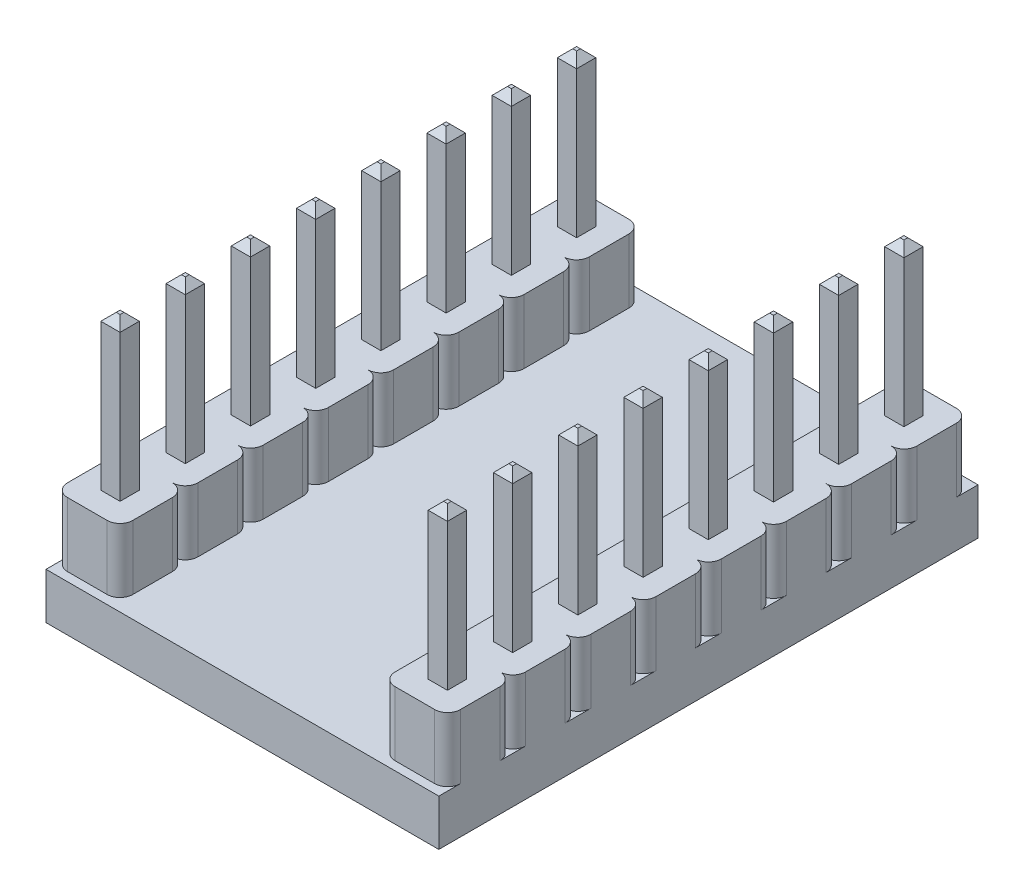
SolidWorks part; units mm, degrees
ref_plane "Plan de face" through (0, 0, 0) normal (0, 0, 1) x (1, 0, 0)
ref_plane "Plan de dessus" through (0, 0, 0) normal (0, 1, 0) x (1, 0, 0)
ref_plane "Plan de droite" through (0, 0, 0) normal (1, 0, 0) x (0, 0, -1)
sketch "Esquisse1" plane through (0, 0, 0) normal (0, 1, 0) x (1, 0, 0)
  line L1 (0, 0) -> (15.3, 0)
  line L2 (0, 0) -> (0, 21)
  line L3 (0, 21) -> (15.3, 21)
  line L4 (15.3, 0) -> (15.3, 21)
  dimension "D1" = 15.3
  dimension "D2" = 21
extrude "Boss.-Extru.1" add sketch "Esquisse1" along normal blind 1.8
sketch "Esquisse2" plane through (0, 1.8, 0) normal (0, 1, 0) x (1, 0, 0)
  line L0 (1.65, 21) -> (1.65, 10.5) construction
  line L1 (0.9, 11.395) -> (1.65, 11.395)
  line L2 (0.9, 11.395) -> (0.9, 12.145)
  line L3 (0.9, 12.145) -> (1.65, 12.145)
  line L4 (1.65, 11.395) -> (1.65, 12.145)
  line L5 (15.3, 21) -> (0, 21) construction
  line L6 (0, 0) -> (15.3, 0) construction
  line L7 (7.65, 21) -> (7.65, 0) construction
  line L8 (15.3, 10.5) -> (0, 10.5) construction
  line L9 (15.3, 0) -> (15.3, 21) construction
  line L10 (0, 21) -> (0, 0) construction
  line L11 (0.9, 16.475) -> (1.65, 16.475)
  line L12 (0.9, 16.475) -> (0.9, 17.225)
  line L13 (0.9, 17.225) -> (1.65, 17.225)
  line L14 (1.65, 16.475) -> (1.65, 17.225)
  line L15 (0.9, 13.935) -> (1.65, 13.935)
  line L16 (0.9, 13.935) -> (0.9, 14.685)
  line L17 (0.9, 14.685) -> (1.65, 14.685)
  line L18 (1.65, 13.935) -> (1.65, 14.685)
  line L20 (1.275, 16.475) -> (1.275, 14.685) construction
  line L21 (1.275, 19.015) -> (1.275, 17.225) construction
  line L22 (1.275, 13.935) -> (1.275, 12.145) construction
  line L23 (0.9, 19.015) -> (1.65, 19.015)
  line L24 (0.9, 19.015) -> (0.9, 19.765)
  line L25 (0.9, 19.765) -> (1.65, 19.765)
  line L26 (1.65, 19.015) -> (1.65, 19.765)
  line L27 (1.65, 9.605) -> (1.65, 8.855)
  line L28 (0.9, 8.855) -> (1.65, 8.855)
  line L29 (0.9, 9.605) -> (0.9, 8.855)
  line L30 (0.9, 9.605) -> (1.65, 9.605)
  line L31 (1.65, 7.065) -> (1.65, 6.315)
  line L32 (0.9, 6.315) -> (1.65, 6.315)
  line L33 (0.9, 7.065) -> (0.9, 6.315)
  line L34 (0.9, 7.065) -> (1.65, 7.065)
  line L35 (1.65, 4.525) -> (1.65, 3.775)
  line L36 (0.9, 3.775) -> (1.65, 3.775)
  line L37 (0.9, 4.525) -> (0.9, 3.775)
  line L38 (0.9, 4.525) -> (1.65, 4.525)
  line L39 (1.65, 1.985) -> (1.65, 1.235)
  line L40 (0.9, 1.235) -> (1.65, 1.235)
  line L41 (0.9, 1.985) -> (0.9, 1.235)
  line L42 (0.9, 1.985) -> (1.65, 1.985)
  line L43 (1.275, 11.395) -> (1.275, 9.605) construction
  line L44 (13.65, 19.015) -> (13.65, 19.765)
  line L45 (14.4, 19.765) -> (13.65, 19.765)
  line L46 (14.4, 19.015) -> (14.4, 19.765)
  line L47 (14.4, 19.015) -> (13.65, 19.015)
  line L48 (13.65, 16.475) -> (13.65, 17.225)
  line L49 (14.4, 17.225) -> (13.65, 17.225)
  line L50 (14.4, 16.475) -> (14.4, 17.225)
  line L51 (14.4, 16.475) -> (13.65, 16.475)
  line L52 (13.65, 13.935) -> (13.65, 14.685)
  line L53 (14.4, 14.685) -> (13.65, 14.685)
  line L54 (14.4, 13.935) -> (14.4, 14.685)
  line L55 (14.4, 13.935) -> (13.65, 13.935)
  line L56 (13.65, 11.395) -> (13.65, 12.145)
  line L57 (14.4, 12.145) -> (13.65, 12.145)
  line L58 (14.4, 11.395) -> (14.4, 12.145)
  line L59 (14.4, 11.395) -> (13.65, 11.395)
  line L60 (14.4, 9.605) -> (13.65, 9.605)
  line L61 (14.4, 9.605) -> (14.4, 8.855)
  line L62 (14.4, 8.855) -> (13.65, 8.855)
  line L63 (13.65, 9.605) -> (13.65, 8.855)
  line L64 (14.4, 7.065) -> (13.65, 7.065)
  line L65 (14.4, 7.065) -> (14.4, 6.315)
  line L66 (14.4, 6.315) -> (13.65, 6.315)
  line L67 (13.65, 7.065) -> (13.65, 6.315)
  line L68 (14.4, 4.525) -> (13.65, 4.525)
  line L69 (14.4, 4.525) -> (14.4, 3.775)
  line L70 (14.4, 3.775) -> (13.65, 3.775)
  line L71 (13.65, 4.525) -> (13.65, 3.775)
  line L72 (14.4, 1.985) -> (13.65, 1.985)
  line L73 (14.4, 1.985) -> (14.4, 1.235)
  line L74 (14.4, 1.235) -> (13.65, 1.235)
  line L75 (13.65, 1.985) -> (13.65, 1.235)
  dimension "D1" = 0.75
  dimension "D2" = 0.9
  dimension "D3" = 0.75
  dimension "D4" = 0.75
  dimension "D5" = 1.79
  dimension "D6" = 0.75
extrude "Boss.-Extru.2" add sketch "Esquisse2" along normal blind 8.5 and the other way blind 2.95
chamfer "Chanfrein1" distance 0.3 angle 45 128 edges at (14.4, 10.3, -1.61) (14.025, 10.3, -1.985) (13.65, 10.3, -1.61) (14.025, 10.3, -1.235) (14.4, 10.3, -4.15) (14.025, 10.3, -4.525) (13.65, 10.3, -4.15) (14.025, 10.3, -3.775) (14.4, 10.3, -6.69) (14.025, 10.3, -7.065) (13.65, 10.3, -6.69) (14.025, 10.3, -6.315) (14.4, 10.3, -9.23) (14.025, 10.3, -9.605) (13.65, 10.3, -9.23) (14.025, 10.3, -8.855) (14.025, 10.3, -11.395) (14.4, 10.3, -11.77) (14.025, 10.3, -12.145) (13.65, 10.3, -11.77) (14.025, 10.3, -13.935) (14.4, 10.3, -14.31) (14.025, 10.3, -14.685) (13.65, 10.3, -14.31) (14.025, 10.3, -16.475) (14.4, 10.3, -16.85) (14.025, 10.3, -17.225) (13.65, 10.3, -16.85) (14.025, 10.3, -19.015) (14.4, 10.3, -19.39) (14.025, 10.3, -19.765) (13.65, 10.3, -19.39) (1.275, 10.3, -1.985) (0.9, 10.3, -1.61) (1.275, 10.3, -1.235) (1.65, 10.3, -1.61) (1.275, 10.3, -4.525) (0.9, 10.3, -4.15) (1.275, 10.3, -3.775) (1.65, 10.3, -4.15) (1.275, 10.3, -7.065) (0.9, 10.3, -6.69) (1.275, 10.3, -6.315) (1.65, 10.3, -6.69) (1.275, 10.3, -9.605) (0.9, 10.3, -9.23) (1.275, 10.3, -8.855) (1.65, 10.3, -9.23) (0.9, 10.3, -19.39) (1.275, 10.3, -19.015) (1.65, 10.3, -19.39) (1.275, 10.3, -19.765) (0.9, 10.3, -14.31) (1.275, 10.3, -13.935) (1.65, 10.3, -14.31) (1.275, 10.3, -14.685) (0.9, 10.3, -16.85) (1.275, 10.3, -16.475) (1.65, 10.3, -16.85) (1.275, 10.3, -17.225) (0.9, 10.3, -11.77) (1.275, 10.3, -11.395) (1.65, 10.3, -11.77) (1.275, 10.3, -12.145) (1.275, -1.15, -12.145) (1.65, -1.15, -11.77) (1.275, -1.15, -11.395) (0.9, -1.15, -11.77) (1.275, -1.15, -17.225) (1.65, -1.15, -16.85) (1.275, -1.15, -16.475) (0.9, -1.15, -16.85) (1.275, -1.15, -14.685) (1.65, -1.15, -14.31) (1.275, -1.15, -13.935) (0.9, -1.15, -14.31) (1.275, -1.15, -19.765) (1.65, -1.15, -19.39) (1.275, -1.15, -19.015) (0.9, -1.15, -19.39) (1.65, -1.15, -9.23) (1.275, -1.15, -8.855) (0.9, -1.15, -9.23) (1.275, -1.15, -9.605) (1.65, -1.15, -6.69) (1.275, -1.15, -6.315) (0.9, -1.15, -6.69) (1.275, -1.15, -7.065) (1.65, -1.15, -4.15) (1.275, -1.15, -3.775) (0.9, -1.15, -4.15) (1.275, -1.15, -4.525) (1.65, -1.15, -1.61) (1.275, -1.15, -1.235) (0.9, -1.15, -1.61) (1.275, -1.15, -1.985) (13.65, -1.15, -19.39) (14.025, -1.15, -19.765) (14.4, -1.15, -19.39) (14.025, -1.15, -19.015) (13.65, -1.15, -16.85) (14.025, -1.15, -17.225) (14.4, -1.15, -16.85) (14.025, -1.15, -16.475) (13.65, -1.15, -14.31) (14.025, -1.15, -14.685) (14.4, -1.15, -14.31) (14.025, -1.15, -13.935) (13.65, -1.15, -11.77) (14.025, -1.15, -12.145) (14.4, -1.15, -11.77) (14.025, -1.15, -11.395) (14.025, -1.15, -8.855) (13.65, -1.15, -9.23) (14.025, -1.15, -9.605) (14.4, -1.15, -9.23) (14.025, -1.15, -6.315) (13.65, -1.15, -6.69) (14.025, -1.15, -7.065) (14.4, -1.15, -6.69) (14.025, -1.15, -3.775) (13.65, -1.15, -4.15) (14.025, -1.15, -4.525) (14.4, -1.15, -4.15) (14.025, -1.15, -1.235) (13.65, -1.15, -1.61) (14.025, -1.15, -1.985) (14.4, -1.15, -1.61)
sketch "Esquisse3" plane through (0, 1.8, 0) normal (0, 1, 0) x (1, 0, 0)
  line L0 (7.65, 0) -> (7.65, 21) construction
  line L1 (13.26, 0.34) -> (14.8, 0.34)
  line L2 (12.76, 0.84) -> (12.76, 2.38)
  line L3 (15.3, 0) -> (15.3, 21) construction
  line L4 (15.3, 0.84) -> (15.3, 2.38)
  line L5 (13.26, 2.88) -> (14.8, 2.88) construction
  line L6 (15.3, 4.92) -> (15.3, 3.38)
  line L7 (12.76, 4.92) -> (12.76, 3.38)
  line L8 (13.26, 5.42) -> (14.8, 5.42) construction
  line L9 (0, 0) -> (15.3, 0) construction
  line L10 (15.3, 21) -> (0, 21) construction
  line L11 (12.76, 1.61) -> (15.3, 1.61) construction
  line L12 (14.4, 1.61) -> (13.65, 1.61) construction
  line L13 (14.4, 1.985) -> (14.4, 1.235) construction
  line L14 (13.65, 1.235) -> (13.65, 1.985) construction
  line L15 (13.26, 7.96) -> (14.8, 7.96) construction
  line L16 (12.76, 5.92) -> (12.76, 7.46)
  line L17 (15.3, 5.92) -> (15.3, 7.46)
  line L18 (15.3, 10) -> (15.3, 8.46)
  line L19 (12.76, 10) -> (12.76, 8.46)
  line L20 (13.26, 10.5) -> (14.8, 10.5)
  line L21 (13.26, 13.04) -> (14.8, 13.04) construction
  line L22 (13.26, 15.58) -> (14.8, 15.58) construction
  line L23 (13.26, 18.12) -> (14.8, 18.12) construction
  line L24 (12.76, 11) -> (12.76, 12.54)
  line L25 (15.3, 11) -> (15.3, 12.54)
  line L26 (15.3, 15.08) -> (15.3, 13.54)
  line L27 (12.76, 15.08) -> (12.76, 13.54)
  line L28 (12.76, 16.08) -> (12.76, 17.62)
  line L29 (15.3, 16.08) -> (15.3, 17.62)
  line L30 (15.3, 20.16) -> (15.3, 18.62)
  line L31 (12.76, 20.16) -> (12.76, 18.62)
  line L32 (13.26, 20.66) -> (14.8, 20.66)
  line L33 (2.04, 18.12) -> (0.5, 18.12) construction
  line L34 (2.04, 15.58) -> (0.5, 15.58) construction
  line L35 (2.04, 13.04) -> (0.5, 13.04) construction
  line L36 (2.04, 7.96) -> (0.5, 7.96) construction
  line L37 (2.04, 5.42) -> (0.5, 5.42) construction
  line L38 (2.04, 2.88) -> (0.5, 2.88) construction
  line L39 (2.04, 20.66) -> (0.5, 20.66)
  line L40 (2.54, 20.16) -> (2.54, 18.62)
  line L41 (0, 20.16) -> (0, 18.62)
  line L42 (0, 16.08) -> (0, 17.62)
  line L43 (2.54, 16.08) -> (2.54, 17.62)
  line L44 (2.54, 15.08) -> (2.54, 13.54)
  line L45 (0, 15.08) -> (0, 13.54)
  line L46 (0, 11) -> (0, 12.54)
  line L47 (2.54, 11) -> (2.54, 12.54)
  line L48 (2.04, 10.5) -> (0.5, 10.5)
  line L49 (2.54, 10) -> (2.54, 8.46)
  line L50 (0, 10) -> (0, 8.46)
  line L51 (0, 5.92) -> (0, 7.46)
  line L52 (2.54, 5.92) -> (2.54, 7.46)
  line L53 (2.54, 4.92) -> (2.54, 3.38)
  line L54 (0, 4.92) -> (0, 3.38)
  line L55 (0, 0.84) -> (0, 2.38)
  line L56 (2.54, 0.84) -> (2.54, 2.38)
  line L57 (2.04, 0.34) -> (0.5, 0.34)
  arc A0 (13.26, 0.34) -> (12.76, 0.84) centre (13.26, 0.84) cw
  arc A1 (14.8, 0.34) -> (15.3, 0.84) centre (14.8, 0.84) ccw
  arc A2 (15.3, 2.38) -> (14.8, 2.88) centre (14.8, 2.38) ccw
  arc A3 (12.76, 2.38) -> (13.26, 2.88) centre (13.26, 2.38) cw
  arc A4 (12.76, 3.38) -> (13.26, 2.88) centre (13.26, 3.38) ccw
  arc A5 (15.3, 3.38) -> (14.8, 2.88) centre (14.8, 3.38) cw
  arc A6 (14.8, 5.42) -> (15.3, 4.92) centre (14.8, 4.92) cw
  arc A7 (13.26, 5.42) -> (12.76, 4.92) centre (13.26, 4.92) ccw
  arc A8 (13.26, 5.42) -> (12.76, 5.92) centre (13.26, 5.92) cw
  arc A9 (14.8, 5.42) -> (15.3, 5.92) centre (14.8, 5.92) ccw
  arc A10 (15.3, 7.46) -> (14.8, 7.96) centre (14.8, 7.46) ccw
  arc A11 (12.76, 7.46) -> (13.26, 7.96) centre (13.26, 7.46) cw
  arc A12 (12.76, 8.46) -> (13.26, 7.96) centre (13.26, 8.46) ccw
  arc A13 (15.3, 8.46) -> (14.8, 7.96) centre (14.8, 8.46) cw
  arc A14 (14.8, 10.5) -> (15.3, 10) centre (14.8, 10) cw
  arc A15 (13.26, 10.5) -> (12.76, 10) centre (13.26, 10) ccw
  arc A16 (13.26, 10.5) -> (12.76, 11) centre (13.26, 11) cw
  arc A17 (14.8, 10.5) -> (15.3, 11) centre (14.8, 11) ccw
  arc A18 (15.3, 12.54) -> (14.8, 13.04) centre (14.8, 12.54) ccw
  arc A19 (12.76, 12.54) -> (13.26, 13.04) centre (13.26, 12.54) cw
  arc A20 (12.76, 13.54) -> (13.26, 13.04) centre (13.26, 13.54) ccw
  arc A21 (15.3, 13.54) -> (14.8, 13.04) centre (14.8, 13.54) cw
  arc A22 (14.8, 15.58) -> (15.3, 15.08) centre (14.8, 15.08) cw
  arc A23 (13.26, 15.58) -> (12.76, 15.08) centre (13.26, 15.08) ccw
  arc A24 (13.26, 15.58) -> (12.76, 16.08) centre (13.26, 16.08) cw
  arc A25 (14.8, 15.58) -> (15.3, 16.08) centre (14.8, 16.08) ccw
  arc A26 (15.3, 17.62) -> (14.8, 18.12) centre (14.8, 17.62) ccw
  arc A27 (12.76, 17.62) -> (13.26, 18.12) centre (13.26, 17.62) cw
  arc A28 (12.76, 18.62) -> (13.26, 18.12) centre (13.26, 18.62) ccw
  arc A29 (15.3, 18.62) -> (14.8, 18.12) centre (14.8, 18.62) cw
  arc A30 (14.8, 20.66) -> (15.3, 20.16) centre (14.8, 20.16) cw
  arc A31 (13.26, 20.66) -> (12.76, 20.16) centre (13.26, 20.16) ccw
  arc A32 (2.04, 20.66) -> (2.54, 20.16) centre (2.04, 20.16) cw
  arc A33 (0.5, 20.66) -> (0, 20.16) centre (0.5, 20.16) ccw
  arc A34 (0, 18.62) -> (0.5, 18.12) centre (0.5, 18.62) ccw
  arc A35 (2.54, 18.62) -> (2.04, 18.12) centre (2.04, 18.62) cw
  arc A36 (2.54, 17.62) -> (2.04, 18.12) centre (2.04, 17.62) ccw
  arc A37 (0, 17.62) -> (0.5, 18.12) centre (0.5, 17.62) cw
  arc A38 (0.5, 15.58) -> (0, 16.08) centre (0.5, 16.08) cw
  arc A39 (2.04, 15.58) -> (2.54, 16.08) centre (2.04, 16.08) ccw
  arc A40 (2.04, 15.58) -> (2.54, 15.08) centre (2.04, 15.08) cw
  arc A41 (0.5, 15.58) -> (0, 15.08) centre (0.5, 15.08) ccw
  arc A42 (0, 13.54) -> (0.5, 13.04) centre (0.5, 13.54) ccw
  arc A43 (2.54, 13.54) -> (2.04, 13.04) centre (2.04, 13.54) cw
  arc A44 (2.54, 12.54) -> (2.04, 13.04) centre (2.04, 12.54) ccw
  arc A45 (0, 12.54) -> (0.5, 13.04) centre (0.5, 12.54) cw
  arc A46 (0.5, 10.5) -> (0, 11) centre (0.5, 11) cw
  arc A47 (2.04, 10.5) -> (2.54, 11) centre (2.04, 11) ccw
  arc A48 (2.04, 10.5) -> (2.54, 10) centre (2.04, 10) cw
  arc A49 (0.5, 10.5) -> (0, 10) centre (0.5, 10) ccw
  arc A50 (0, 8.46) -> (0.5, 7.96) centre (0.5, 8.46) ccw
  arc A51 (2.54, 8.46) -> (2.04, 7.96) centre (2.04, 8.46) cw
  arc A52 (2.54, 7.46) -> (2.04, 7.96) centre (2.04, 7.46) ccw
  arc A53 (0, 7.46) -> (0.5, 7.96) centre (0.5, 7.46) cw
  arc A54 (0.5, 5.42) -> (0, 5.92) centre (0.5, 5.92) cw
  arc A55 (2.04, 5.42) -> (2.54, 5.92) centre (2.04, 5.92) ccw
  arc A56 (2.04, 5.42) -> (2.54, 4.92) centre (2.04, 4.92) cw
  arc A57 (0.5, 5.42) -> (0, 4.92) centre (0.5, 4.92) ccw
  arc A58 (0, 3.38) -> (0.5, 2.88) centre (0.5, 3.38) ccw
  arc A59 (2.54, 3.38) -> (2.04, 2.88) centre (2.04, 3.38) cw
  arc A60 (2.54, 2.38) -> (2.04, 2.88) centre (2.04, 2.38) ccw
  arc A61 (0, 2.38) -> (0.5, 2.88) centre (0.5, 2.38) cw
  arc A62 (0.5, 0.34) -> (0, 0.84) centre (0.5, 0.84) cw
  arc A63 (2.04, 0.34) -> (2.54, 0.84) centre (2.04, 0.84) ccw
  point P0 (14.025, 2.4935)
  point P37 (14.025, 5.0435)
  point P40 (14.4, 9.23)
  point P61 (14.025, 5.7965)
  point P62 (14.025, 8.3465)
  point P103 (14.025, 12.6535)
  point P104 (14.025, 15.2035)
  point P105 (14.4, 11.77)
  point P106 (14.025, 15.9565)
  point P107 (14.025, 18.5065)
  point P190 (1.275, 18.5065)
  point P191 (1.275, 15.9565)
  point P192 (0.9, 11.77)
  point P193 (1.275, 15.2035)
  point P194 (1.275, 12.6535)
  point P195 (1.275, 8.3465)
  point P196 (1.275, 5.7965)
  point P197 (0.9, 9.23)
  point P198 (1.275, 5.0435)
  point P199 (1.275, 2.4935)
  dimension "D2" = 2.54
  dimension "D3" = 0.5
  dimension "D1" = 2.54
extrude "Boss.-Extru.4" add sketch "Esquisse3" along normal blind 2.5 contours L20 A15 L19 A12 A11 L16 A8 A7 L7 A4 A3 L2 A0 L1 A1 L4 A2 A5 L6 A6 A9 L17 A10 A13 L18 A14 | L32 A31 L31 A28 A27 L28 A24 A23 L27 A20 A19 L24 A16 L20 A17 L25 A18 A21 L26 A22 A25 L29 A26 A29 L30 A30 | L48 A47 L47 A44 A43 L44 A40 A39 L43 A36 A35 L40 A32 L39 A33 L41 A34 A37 L42 A38 A41 L45 A42 A45 L46 A46 | L57 A63 L56 A60 A59 L53 A56 A55 L52 A52 A51 L49 A48 L48 A49 L50 A50 A53 L51 A54 A57 L54 A58 A61 L55 A62
fillet "Congé1" radius 0.5 64 edges at (1.65, 0, -1.61) (1.275, 0, -1.985) (1.275, 0, -1.235) (0.9, 0, -1.61) (14.4, 0, -1.61) (14.025, 0, -1.235) (13.65, 0, -1.61) (14.025, 0, -1.985) (14.4, 0, -4.15) (14.025, 0, -3.775) (13.65, 0, -4.15) (14.025, 0, -4.525) (14.4, 0, -6.69) (14.025, 0, -6.315) (13.65, 0, -6.69) (14.025, 0, -7.065) (14.4, 0, -9.23) (14.025, 0, -8.855) (13.65, 0, -9.23) (14.025, 0, -9.605) (14.025, 0, -11.395) (13.65, 0, -11.77) (14.025, 0, -12.145) (14.4, 0, -11.77) (14.025, 0, -13.935) (13.65, 0, -14.31) (14.025, 0, -14.685) (14.4, 0, -14.31) (14.025, 0, -16.475) (13.65, 0, -16.85) (14.025, 0, -17.225) (14.4, 0, -16.85) (14.025, 0, -19.015) (13.65, 0, -19.39) (14.025, 0, -19.765) (14.4, 0, -19.39) (1.275, 0, -9.605) (1.65, 0, -9.23) (1.275, 0, -8.855) (0.9, 0, -9.23) (0.9, 0, -19.39) (1.275, 0, -19.765) (1.65, 0, -19.39) (1.275, 0, -19.015) (0.9, 0, -14.31) (1.275, 0, -14.685) (1.65, 0, -14.31) (1.275, 0, -13.935) (0.9, 0, -16.85) (1.275, 0, -17.225) (1.65, 0, -16.85) (1.275, 0, -16.475) (0.9, 0, -11.77) (1.275, 0, -12.145) (1.65, 0, -11.77) (1.275, 0, -11.395) (0.9, 0, -4.15) (1.275, 0, -4.525) (1.275, 0, -3.775) (1.65, 0, -4.15) (1.275, 0, -6.315) (1.65, 0, -6.69) (1.275, 0, -7.065) (0.9, 0, -6.69)
